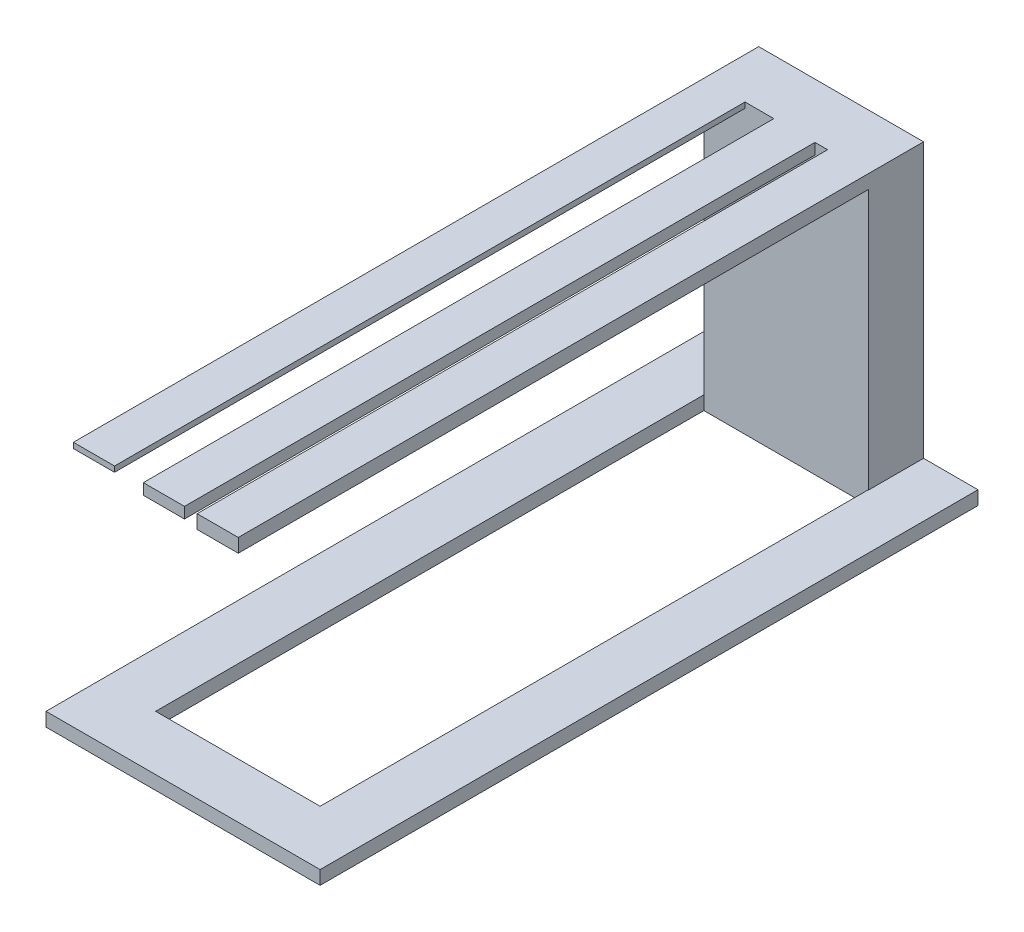
SolidWorks part; units mm, degrees
ref_plane "Front Plane" through (0, 0, 0) normal (0, 0, 1) x (1, 0, 0)
ref_plane "Top Plane" through (0, 0, 0) normal (0, 1, 0) x (1, 0, 0)
ref_plane "Right Plane" through (0, 0, 0) normal (1, 0, 0) x (0, 0, -1)
sketch "Sketch1" plane through (0, 0, 0) normal (0, 1, 0) x (1, 0, 0)
  line L0 (32.7004, 19.4817) -> (52.7004, 19.4817)
  line L1 (-27.2996, 19.4817) -> (32.7004, 19.4817)
  line L2 (-27.2996, 19.4817) -> (-27.2996, -180.5183)
  line L3 (-27.2996, -180.5183) -> (32.7004, -180.5183)
  line L4 (32.7004, 19.4817) -> (32.7004, -180.5183)
  line L5 (52.7004, 19.4817) -> (52.7004, 39.4817)
  line L6 (-27.2996, -180.5183) -> (-47.2996, -180.5183)
  line L7 (52.7004, 39.4817) -> (-47.2996, 39.4817)
  line L8 (52.7004, 39.4817) -> (52.7004, -200.5183)
  line L9 (52.7004, -200.5183) -> (-47.2996, -200.5183)
  line L10 (-47.2996, 39.4817) -> (-47.2996, -200.5183)
  line L11 (-27.2996, -180.5183) -> (-27.2996, -200.5183)
  dimension "D1" = 60
  dimension "D2" = 200
  dimension "D3" = 20
  dimension "D4" = 20
  dimension "D5" = 20
  dimension "D6" = 20
extrude "Boss-Extrude1" add sketch "Sketch1" along normal blind 5 contours L3 L11 L9 L8 L0 L4 | L7 L10 L6 L2 L1 L0 L5 | L11 L6 L10 L9
sketch "Sketch2" plane through (0, 5, 0) normal (0, 1, 0) x (1, 0, 0)
  line L0 (52.7004, 39.4817) -> (-47.2996, 39.4817) construction
  line L1 (-27.2996, 19.4817) -> (32.8371, 19.4817)
  line L2 (-27.2996, 19.4817) -> (-27.2996, 39.4817)
  line L3 (-27.2996, 39.4817) -> (32.8371, 39.4817)
  line L4 (32.8371, 19.4817) -> (32.8371, 39.4817)
extrude "Boss-Extrude2" add sketch "Sketch2" along normal blind 100
sketch "Sketch3" plane through (0, 0, -19.4817) normal (0, 0, 1) x (1, 0, 0)
  line L0 (-27.2996, 105) -> (32.8371, 105) construction
  line L1 (-27.2996, 105) -> (-12.2996, 105)
  line L2 (-27.2996, 105) -> (-27.2996, 103)
  line L3 (-27.2996, 103) -> (-12.2996, 103)
  line L4 (-12.2996, 105) -> (-12.2996, 103)
  line L5 (32.8371, 105) -> (17.8371, 105)
  line L6 (32.8371, 105) -> (32.8371, 100)
  line L7 (32.8371, 100) -> (17.8371, 100)
  line L8 (17.8371, 105) -> (17.8371, 100)
  line L9 (13.2134, 105) -> (-1.7866, 105)
  line L10 (13.2134, 105) -> (13.2134, 101)
  line L11 (13.2134, 101) -> (-1.7866, 101)
  line L12 (-1.7866, 105) -> (-1.7866, 101)
  dimension "D1" = 15
  dimension "D2" = 2
  dimension "D3" = 15
  dimension "D4" = 4
  dimension "D5" = 5
  dimension "D6" = 15
extrude "Boss-Extrude3" add sketch "Sketch3" along normal blind 230
